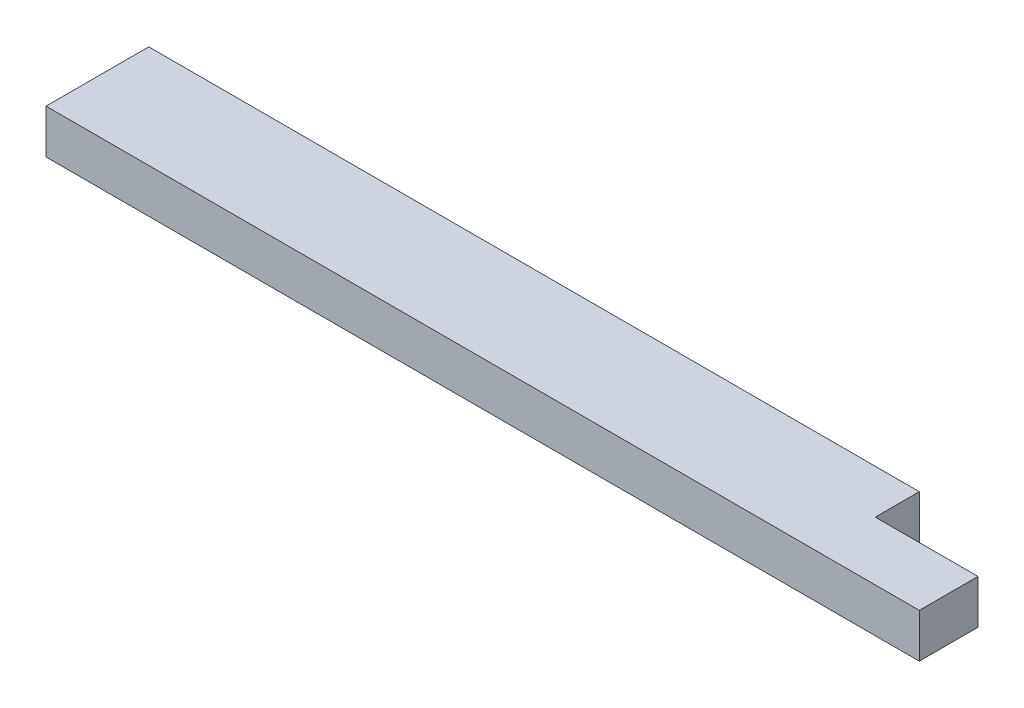
SolidWorks part; units mm, degrees
material "Pine"
ref_plane "Front Plane" through (0, 0, 0) normal (0, 0, 1) x (1, 0, 0)
ref_plane "Top Plane" through (0, 0, 0) normal (0, 1, 0) x (1, 0, 0)
ref_plane "Right Plane" through (0, 0, 0) normal (1, 0, 0) x (0, 0, -1)
sketch "Sketch1" plane through (0, 0, 0) normal (0, 1, 0) x (1, 0, 0)
  line L1 (0, 0) -> (755.65, 0)
  line L2 (0, 0) -> (0, 88.9)
  line L3 (0, 88.9) -> (755.65, 88.9)
  line L4 (755.65, 0) -> (755.65, 88.9)
  dimension "D1" = 88.9
  dimension "D2" = 755.65
extrude "Boss-Extrude1" add sketch "Sketch1" along normal blind 38.1
sketch "Sketch2" plane through (0, 0, 0) normal (0, -1, 0) x (1, 0, 0)
  line L0 (755.65, -88.9) -> (0, -88.9) construction
  line L1 (755.65, -50.8) -> (666.75, -50.8)
  line L2 (755.65, -88.9) -> (755.65, -50.8)
  line L4 (666.75, -88.9) -> (666.75, -50.8)
  line L5 (755.65, -88.9) -> (666.75, -88.9)
  line L7 (755.65, 0) -> (755.65, -88.9) construction
  line L8 (0, 0) -> (755.65, 0) construction
  dimension "D1" = 666.75
  dimension "D2" = 50.8
extrude "Cut-Extrude1" cut sketch "Sketch2" against normal through all
